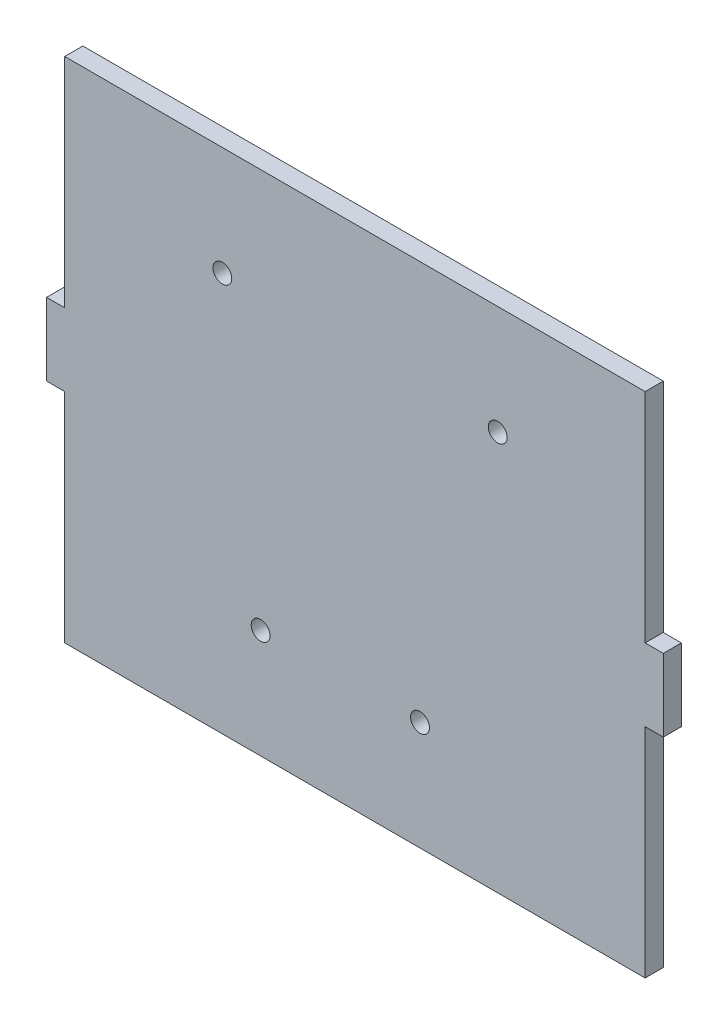
SolidWorks part; units mm, degrees
ref_plane "Front Plane" through (0, 0, 0) normal (0, 0, 1) x (1, 0, 0)
ref_plane "Top Plane" through (0, 0, 0) normal (0, 1, 0) x (1, 0, 0)
ref_plane "Right Plane" through (0, 0, 0) normal (1, 0, 0) x (0, 0, -1)
sketch "Sketch1" plane through (0, 0, 0) normal (0, 0, 1) x (1, 0, 0)
  line L1 (0, 0) -> (101.6, 0)
  line L2 (0, 0) -> (0, 88.9)
  line L3 (0, 88.9) -> (101.6, 88.9)
  line L4 (101.6, 0) -> (101.6, 88.9)
  dimension "D1" = 88.9
  dimension "D2" = 101.6
extrude "Boss-Extrude1" add sketch "Sketch1" along normal blind 3.175
sketch "Sketch2" plane through (0, 0, 3.175) normal (0, 0, 1) x (1, 0, 0)
  line L0 (0, 88.9) -> (0, 0) construction
  line L1 (0, 50.8) -> (-3.175, 50.8)
  line L2 (0, 50.8) -> (0, 38.1)
  line L3 (0, 38.1) -> (-3.175, 38.1)
  line L4 (-3.175, 50.8) -> (-3.175, 38.1)
  line L5 (50.8, 88.9) -> (50.8, 0) construction
  line L6 (101.6, 88.9) -> (0, 88.9) construction
  line L7 (0, 0) -> (101.6, 0) construction
  line L8 (101.6, 50.8) -> (101.6, 38.1)
  line L9 (101.6, 38.1) -> (104.775, 38.1)
  line L10 (101.6, 50.8) -> (104.775, 50.8)
  line L11 (104.775, 50.8) -> (104.775, 38.1)
  point P6 (0, 44.45)
  point P7 (-3.175, 44.45)
  dimension "D1" = 3.175
  dimension "D2" = 12.7
extrude "Boss-Extrude2" add sketch "Sketch2" against normal blind 3.175
sketch "Sketch3" plane through (0, 0, 3.175) normal (0, 0, 1) x (1, 0, 0)
  line L0 (101.6, 88.9) -> (0, 88.9) construction
  line L3 (0, 38.1) -> (0, 0) construction
  circle A0 centre (27.59, 69.85) radius 1.65
  circle A1 centre (75.79, 69.85) radius 1.65
  circle A2 centre (62.19, 19.05) radius 1.65
  circle A3 centre (34.29, 19.05) radius 1.65
  point P8 (0, 0)
  point P9 (0, 0)
  point P10 (0, 0)
  point P11 (0, 0)
  point P12 (69.422, 47.7432)
  point P13 (24.7748, 79.8472)
  point P14 (3.5909, 79.8647)
  dimension "D1" = 3.3
  dimension "D2" = 27.9
  dimension "D3" = 48.2
  dimension "D4" = 50.8
  dimension "D5" = 13.6
  dimension "D6" = 19.05
  dimension "D7" = 34.29
extrude "Cut-Extrude1" cut sketch "Sketch3" against normal through all
